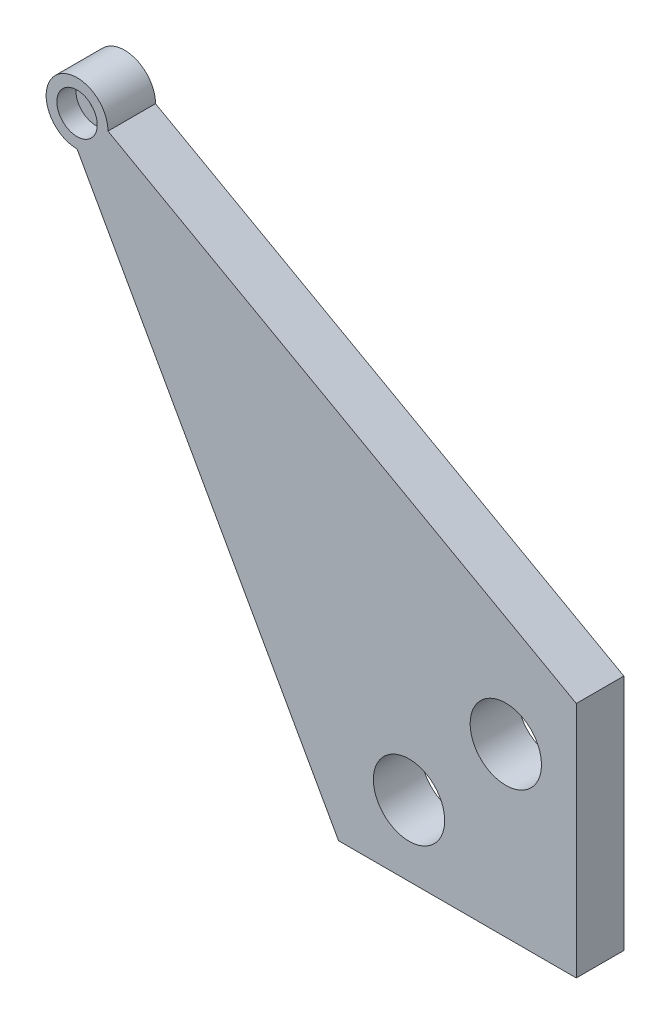
SolidWorks part; units mm, degrees
ref_plane "Plano frontal" through (0, 0, 0) normal (0, 0, 1) x (1, 0, 0)
ref_plane "Plano superior" through (0, 0, 0) normal (0, 1, 0) x (1, 0, 0)
ref_plane "Plano direito" through (0, 0, 0) normal (1, 0, 0) x (0, 0, -1)
sketch "Esboço3" plane through (0, 0, 0) normal (0, 0, 1) x (1, 0, 0)
  line L0 (-62.966, 0) -> (106.6858, 0) construction
  line L1 (0, 69.7378) -> (0, -73.302) construction
  line L2 (0, 50) -> (98.5, 105)
  line L3 (0, 0) -> (50, 0)
  line L4 (0, 0) -> (0, 50)
  line L7 (50, 0) -> (105, 98.5)
  arc A0 (105, 98.5) -> (98.5, 105) centre (105, 105) ccw
  dimension "D4" = 105
  dimension "D5" = 13
  dimension "D3" = 105
extrude "Ressalto-extrusão2" add sketch "Esboço3" along normal mid plane 10
sketch "Esboço4" plane through (0, 0, 5) normal (0, 0, 1) x (1, 0, 0)
  circle A0 centre (105, 105) radius 4.25
  arc A1 (105, 98.5) -> (98.5, 105) centre (105, 105) ccw construction
  dimension "D1" = 8.5
extrude "Corte-extrusão1" cut sketch "Esboço4" against normal blind 4 contours A0
sketch "Esboço5" plane through (0, 0, 1) normal (0, 0, 1) x (1, 0, 0)
  circle A0 centre (105, 105) radius 1.5
  circle A1 centre (105, 105) radius 4.25 construction
extrude "Corte-extrusão2" cut sketch "Esboço5" against normal through all
sketch "Esboço6" plane through (0, 0, 5) normal (0, 0, 1) x (1, 0, 0)
  line L0 (-26.6702, 0) -> (72.5742, 0) construction
  line L1 (0, 62.2144) -> (0, -11.4301) construction
  line L2 (0, 50) -> (63.2897, 50) construction
  line L3 (50, 0) -> (50, 50) construction
  line L4 (0, 50) -> (14.8256, 35.1744) construction
  line L5 (14.8256, 35.1744) -> (35.1744, 14.8256) construction
  line L6 (35.1744, 14.8256) -> (50, 0) construction
  line L7 (0, 0) -> (50, 50) construction
  circle A0 centre (14.8256, 35.1744) radius 7.5
  circle A1 centre (35.1744, 14.8256) radius 7.5
  dimension "D1" = 15
  dimension "D2" = 15
extrude "Corte-extrusão3" cut sketch "Esboço6" against normal through all
mirror "Espelhar1" about plane through (0, 0, 5) normal (0, 1, 0) of bodies 105
mirror "Espelhar2" about plane through (0, 0, 5) normal (1, 0, 0) of bodies 106 105
delete or keep bodies "Corpo-Excluir/Manter 1" type delete bodies bodies 105 106 107
